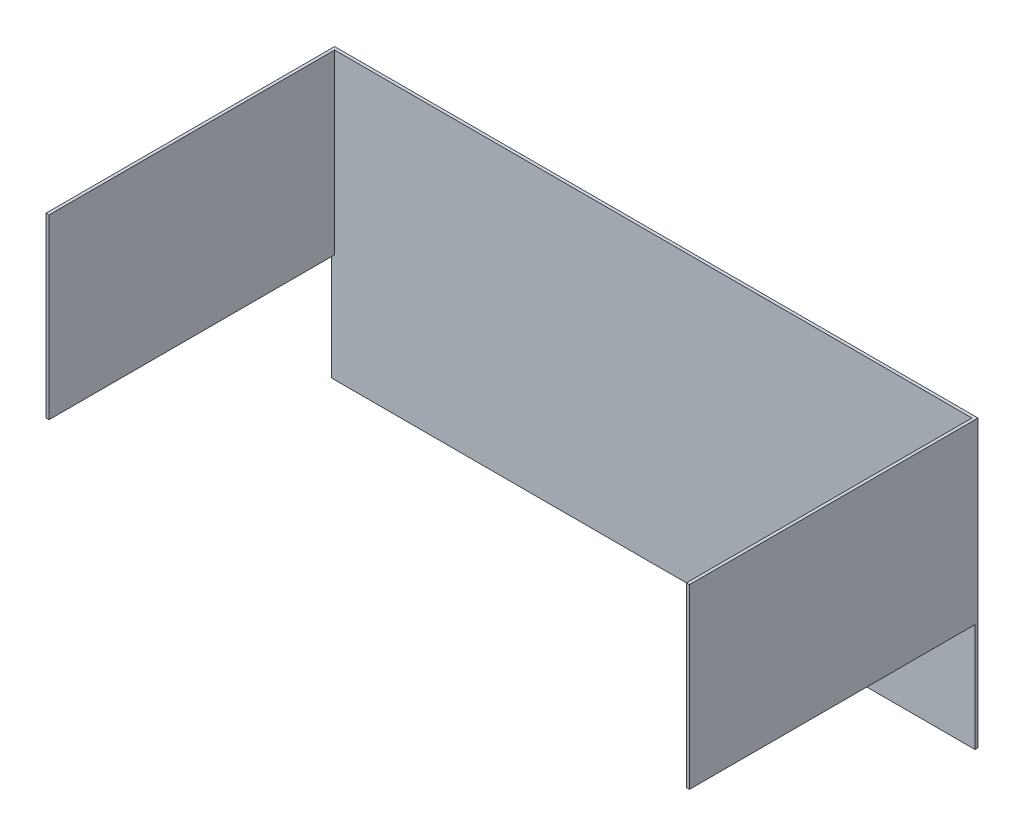
SolidWorks part; units mm, degrees
material "PC High Viscosity"
ref_plane "Front Plane" through (0, 0, 0) normal (0, 0, 1) x (1, 0, 0)
ref_plane "Top Plane" through (0, 0, 0) normal (0, 1, 0) x (1, 0, 0)
ref_plane "Right Plane" through (0, 0, 0) normal (1, 0, 0) x (0, 0, -1)
sketch "Sketch1" plane through (0, 0, 0) normal (0, 1, 0) x (1, 0, 0)
  line L2 (-339.725, -152.4) -> (-339.725, 152.4)
  line L3 (-339.725, 152.4) -> (339.725, 152.4)
  line L4 (339.725, -152.4) -> (339.725, 152.4)
  line L5 (-339.725, -152.4) -> (339.725, 152.4) construction
  line L6 (-339.725, 152.4) -> (339.725, -152.4) construction
  point P0 (0, 0)
  dimension "D1" = 679.45
  dimension "D2" = 304.8
extrude "Extrude-Thin1" add sketch "Sketch1" along normal blind 301.625 thin
sketch "Sketch2" plane through (-336.55, 0, 0) normal (1, 0, 0) x (0, 0, -1)
  line L0 (-152.4, 114.3) -> (149.225, 114.3)
  line L1 (-152.4, 301.625) -> (-152.4, 0) construction
  line L2 (149.225, 301.625) -> (149.225, 0) construction
  line L3 (149.225, 114.3) -> (149.225, 0)
  line L4 (149.225, 0) -> (-152.4, 0)
  line L5 (-152.4, 0) -> (-152.4, 114.3)
  dimension "D1" = 114.3
extrude "Cut-Extrude1" cut sketch "Sketch2" against normal through all both and the other way through all
